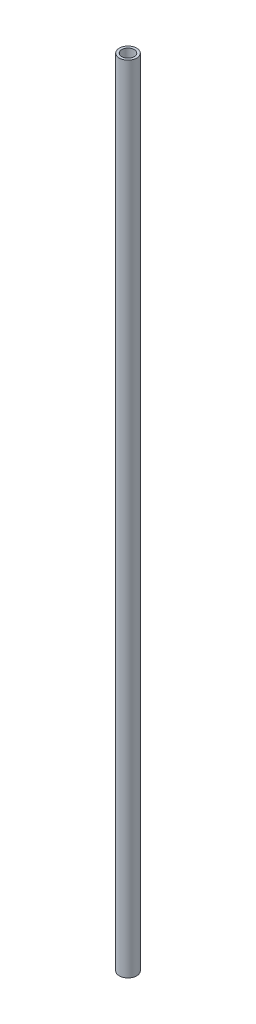
SolidWorks part; units mm, degrees
ref_plane "Front Plane" through (0, 0, 0) normal (0, 0, 1) x (1, 0, 0)
ref_plane "Top Plane" through (0, 0, 0) normal (0, 1, 0) x (1, 0, 0)
ref_plane "Right Plane" through (0, 0, 0) normal (1, 0, 0) x (0, 0, -1)
sketch "Sketch1" plane through (0, 0, 0) normal (0, 1, 0) x (1, 0, 0)
  circle A0 centre (0, 0) radius 9.525
  circle A1 centre (0, 0) radius 13.335
  dimension "D1" = 26.67
  dimension "D2" = 19.05
extrude "Boss-Extrude1" add sketch "Sketch1" along normal blind 1219.2
